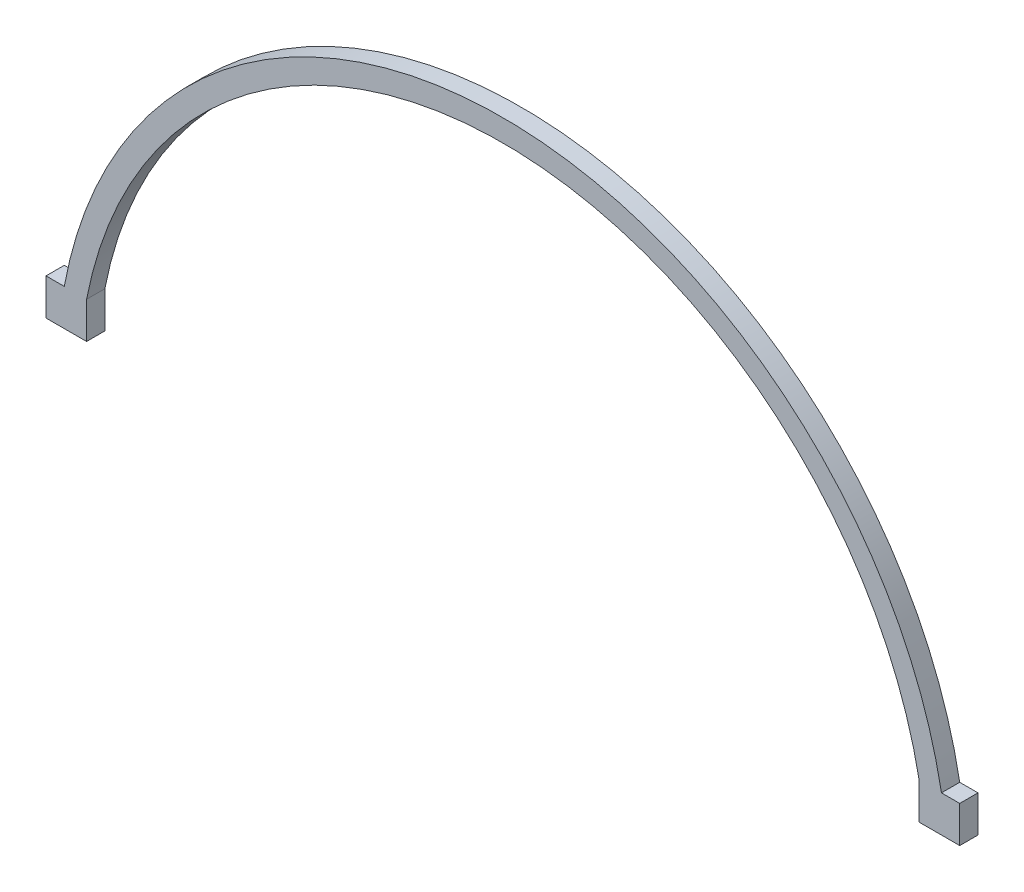
SolidWorks part; units mm, degrees
ref_plane "Front" through (0, 0, 0) normal (0, 0, 1) x (1, 0, 0)
ref_plane "Top" through (0, 0, 0) normal (0, 1, 0) x (1, 0, 0)
ref_plane "Right" through (0, 0, 0) normal (1, 0, 0) x (0, 0, -1)
sketch "Sketch1" plane through (0, 0, 0) normal (0, 0, 1) x (1, 0, 0)
  line L0 (-76.2, 0) -> (76.2, 0) construction
  line L1 (0, 0) -> (0, 63.5) construction
  line L2 (-76.2, 0) -> (-72.3231, 0)
  line L3 (76.2, 0) -> (72.3231, 0)
  arc A0 (-76.2, 0) -> (76.2, 0) centre (0, -13.97) cw
  arc A1 (-72.3231, 0) -> (72.3231, 0) centre (0, -13.97) cw
  arc A2 (-72.4525, -0.687) -> (72.4525, -0.687) centre (0, -13.97) cw construction
  point P4 (0, 0)
  dimension "D1" = 152.4
  dimension "D2" = 63.5
  dimension "D3" = 3.81
extrude "Boss-Extrude1" add sketch "Sketch1" along normal blind 3.175 contours A1 L3 A0 L2
sketch "Sketch2" plane through (0, 0, 0) normal (0, -1, 0) x (1, 0, 0)
  line L0 (76.2, 3.175) -> (76.2, 0) construction
  line L1 (72.3231, 0) -> (79.375, 0)
  line L2 (72.3231, 0) -> (72.3231, 3.175)
  line L3 (72.3231, 3.175) -> (79.375, 3.175)
  line L4 (79.375, 0) -> (79.375, 3.175)
  line L5 (76.2, 3.175) -> (72.3231, 3.175) construction
  line L6 (0, 0) -> (0, 87.8542) construction
  line L7 (-72.3231, 0) -> (72.3231, 0) construction
  line L8 (-72.3231, 3.175) -> (-79.375, 3.175)
  line L9 (-79.375, 0) -> (-79.375, 3.175)
  line L10 (-72.3231, 0) -> (-79.375, 0)
  line L11 (-72.3231, 0) -> (-72.3231, 3.175)
  dimension "D1" = 3.175
extrude "Boss-Extrude2" add sketch "Sketch2" along normal blind 6.35
